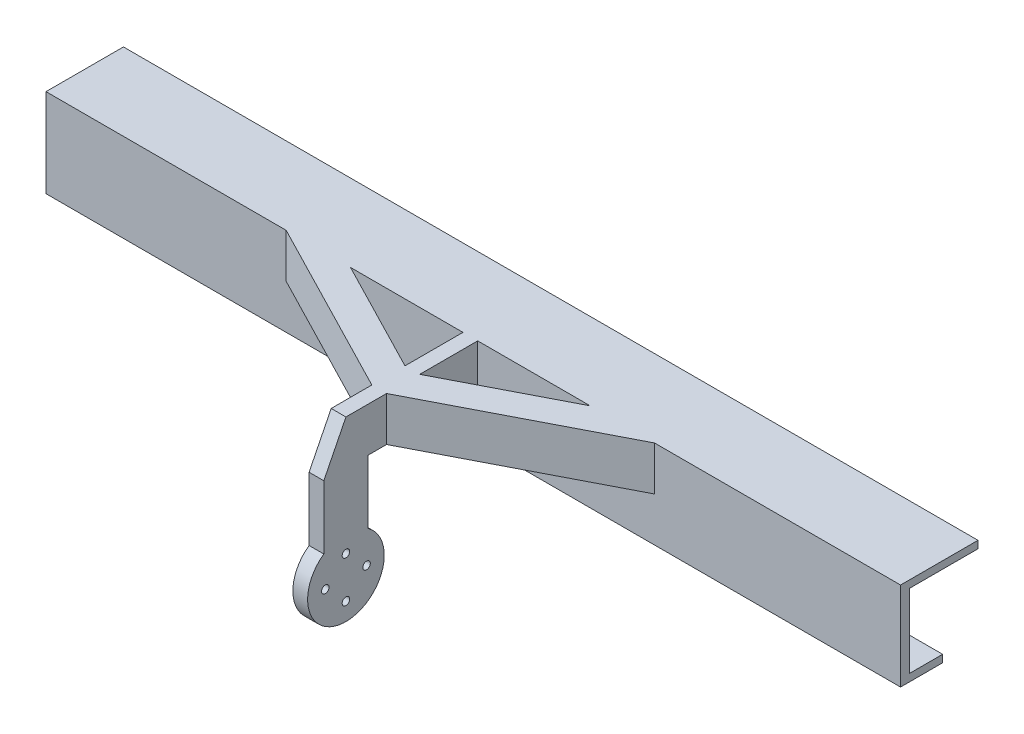
SolidWorks part; units mm, degrees
ref_plane "Front Plane" through (0, 0, 0) normal (0, 0, 1) x (1, 0, 0)
ref_plane "Top Plane" through (0, 0, 0) normal (0, 1, 0) x (1, 0, 0)
ref_plane "Right Plane" through (0, 0, 0) normal (1, 0, 0) x (0, 0, -1)
ref_plane "Plane1" through (0, 0, 1.7155) normal (0, 0, 1) x (1, 0, 0)
sketch "Sketch2" plane through (0, 0, 1.7155) normal (0, 0, 1) x (1, 0, 0)
  line L0 (145, 0) -> (-145, 0) construction
  line L1 (145, 15) -> (-145, 15)
  line L3 (145, -15) -> (-145, -15)
  line L5 (140, 12.5) -> (-140, 12.5)
  line L7 (140, -12.5) -> (-140, -12.5)
  line L12 (145, 15) -> (145, -15)
  line L13 (-140, 12.5) -> (-140, -12.5)
  line L14 (-145, 15) -> (-145, -15)
  line L15 (140, 12.5) -> (140, -12.5)
  dimension "D1" = 25
  dimension "D2" = 30
  dimension "D3" = 5
  dimension "D4" = 290
  dimension "D6" = 5
extrude "Boss-Extrude1" add sketch "Sketch2" along normal blind 23.28
sketch "Sketch3" plane through (0, 0, 24.9955) normal (0, 0, 1) x (1, 0, 0)
  line L1 (145, 15) -> (-145, 15)
  line L2 (145, 15) -> (145, -15)
  line L3 (145, -15) -> (-145, -15)
  line L4 (-145, 15) -> (-145, -15)
extrude "Boss-Extrude2" add sketch "Sketch3" along normal blind 3
sketch "Sketch4" plane through (145, 0, 0) normal (1, 0, 0) x (0, 0, -1)
  line L0 (-27.9955, -15) -> (-27.9955, 15) construction
  line L1 (-1.7155, -12.5) -> (-24.9955, -12.5)
  line L2 (-1.7155, -12.5) -> (-1.7155, 12.5)
  line L3 (-1.7155, 12.5) -> (-24.9955, 12.5)
  line L4 (-24.9955, -12.5) -> (-24.9955, 12.5)
  line L5 (-27.9955, -15) -> (-1.7155, -15) construction
  line L7 (-1.7155, -15) -> (-1.7155, 15) construction
  line L10 (-24.9955, 12.5) -> (-1.7155, 12.5) construction
  dimension "D1" = 3
  dimension "D2" = 2.5
extrude "Cut-Extrude1" cut sketch "Sketch4" against normal through all and the other way through all
ref_plane "Plane3" through (-0.5, 0, 0) normal (-1, 0, 0) x (0, 0, 1)
sketch "Sketch5" plane through (-0.5, 0, 0) normal (1, 0, 0) x (0, 0, -1)
  line L4 (-27.9955, 0) -> (-27.9955, 15)
  line L5 (-27.9955, 15) -> (-72.7155, 15)
  line L6 (-65.2155, 0) -> (-65.2155, -21.5316)
  line L7 (-27.9955, 0) -> (-65.2155, 0)
  line L8 (-80.2155, 0) -> (-80.2155, -21.5316)
  line L9 (-80.2155, 0) -> (-72.7155, 15)
  line L10 (-27.9955, -15) -> (-27.9955, 15) construction
  line L11 (-27.9955, 15) -> (-1.7155, 15) construction
  arc A0 (-80.2155, -21.5316) -> (-65.2155, -21.5316) centre (-72.7155, -32.15) ccw
  dimension "D3" = 13
  dimension "D4" = 52.22
  dimension "D1" = 15
  dimension "D2" = 15
  dimension "D5" = 47.15
  dimension "D6" = 13.4164
extrude "Boss-Extrude3" add sketch "Sketch5" along normal blind 2 and the other way blind 3
sketch "Sketch6" plane through (-3.5, 0, 0) normal (1, 0, 0) x (0, 0, -1)
  circle A0 centre (-72.7155, -32.15) radius 10
  arc A1 (-80.2155, -21.5316) -> (-65.2155, -21.5316) centre (-72.7155, -32.15) ccw construction
  dimension "D1" = 20
extrude "Cut-Extrude2" cut sketch "Sketch6" along normal blind 2
sketch "Sketch7" plane through (-3.5, 0, 0) normal (-1, 0, 0) x (0, 0, 1)
  line L0 (72.7155, -27.3874) -> (72.7155, -79.0243) construction
  line L1 (65.2155, -21.5316) -> (65.2155, 0) construction
  line L6 (80.2155, 0) -> (80.2155, -21.5316) construction
  line L7 (-104.8443, -32.15) -> (-53.4231, -32.15) construction
  circle A0 centre (72.7155, -25.15) radius 1.275
  circle A1 centre (79.7155, -32.15) radius 1.275
  circle A2 centre (72.7155, -39.15) radius 1.275
  circle A3 centre (65.7155, -32.15) radius 1.275
  arc A5 (65.2155, -21.5316) -> (80.2155, -21.5316) centre (72.7155, -32.15) ccw construction
  point P32 (72.7155, -32.15)
  dimension "D1" = 2.55
  dimension "D5" = 2.55
  dimension "D6" = 2.55
  dimension "D7" = 2.55
  dimension "D2" = 7
  dimension "D3" = 7
  dimension "D4" = 7
  dimension "D8" = 7
extrude "Cut-Extrude3" cut sketch "Sketch7" against normal blind 10
sketch "Sketch8" plane through (0, 0, 1.7155) normal (0, 0, -1) x (-1, 0, 0)
  line L1 (-145, -15) -> (145, -15)
  line L2 (-145, -15) -> (-145, -12.5)
  line L3 (-145, -12.5) -> (145, -12.5)
  line L4 (145, -15) -> (145, -12.5)
extrude "Cut-Extrude4" cut sketch "Sketch8" against normal blind 12
sketch "Sketch9" plane through (0, 15, 0) normal (0, 1, 0) x (1, 0, 0)
  line L0 (-3.5, -58.9222) -> (-63.5, -27.9955)
  line L3 (-3.5, -47.672) -> (-41.6737, -27.9955)
  line L4 (-3.5, -27.9955) -> (-3.5, -72.7155) construction
  line L5 (-3.5, -58.9222) -> (-3.5, -47.672)
  line L6 (-3.5, -27.9955) -> (-145, -27.9955) construction
  line L7 (-63.5, -27.9955) -> (-41.6737, -27.9955)
  line L8 (-1, -64.4544) -> (-1, -20.3652) construction
  line L9 (1.5, -27.9955) -> (1.5, -72.7155) construction
  line L10 (61.5, -27.9955) -> (39.6737, -27.9955)
  line L11 (1.5, -58.9222) -> (1.5, -47.672)
  line L12 (1.5, -47.672) -> (39.6737, -27.9955)
  line L13 (1.5, -58.9222) -> (61.5, -27.9955)
  dimension "D1" = 60
  dimension "D2" = 10
extrude "Boss-Extrude4" add sketch "Sketch9" against normal up to surface (15 mm away) up to face at (-1, 0, 46.6055)
